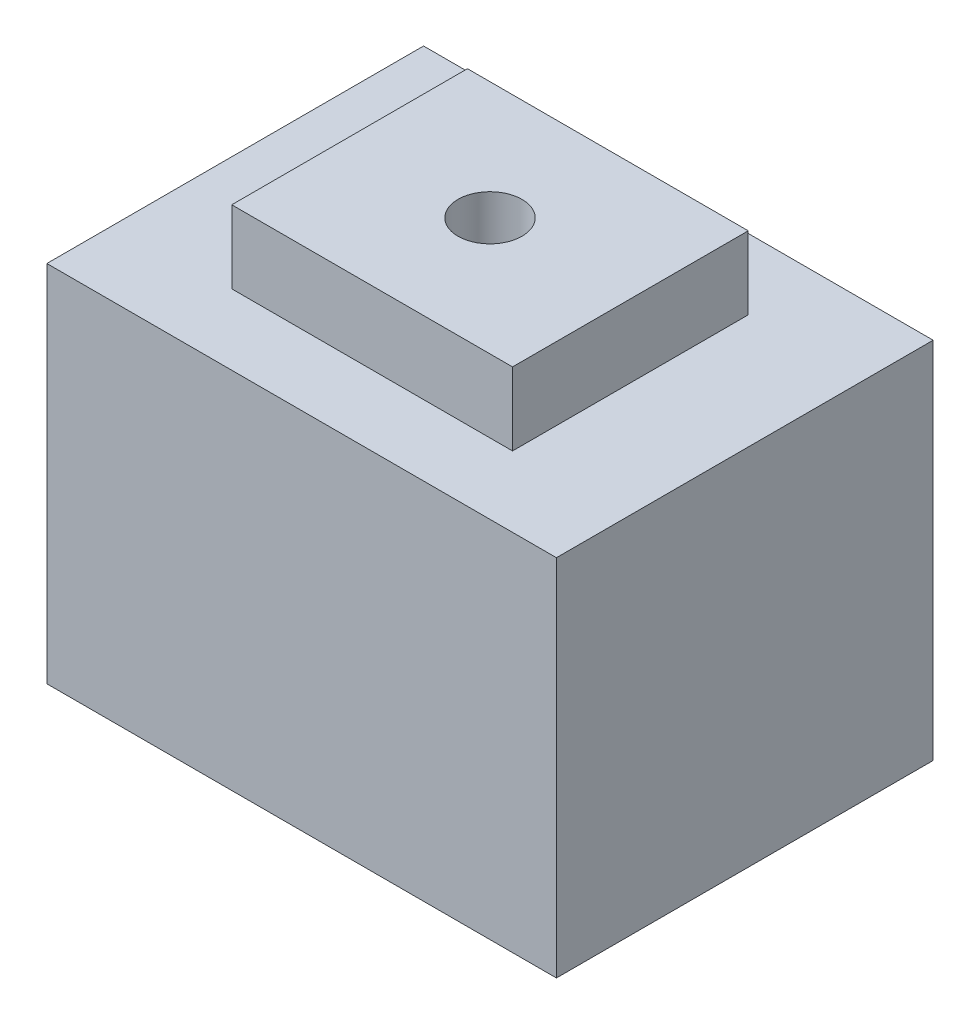
SolidWorks part; units mm, degrees
ref_plane "Front Plane" through (0, 0, 0) normal (0, 0, 1) x (1, 0, 0)
ref_plane "Top Plane" through (0, 0, 0) normal (0, 1, 0) x (1, 0, 0)
ref_plane "Right Plane" through (0, 0, 0) normal (1, 0, 0) x (0, 0, -1)
sketch "Sketch3" plane through (0, 0, 0) normal (0, 1, 0) x (1, 0, 0)
  line L1 (-35, -25.8732) -> (35, -25.8732)
  line L2 (-35, -25.8732) -> (-35, 25.8732)
  line L3 (-35, 25.8732) -> (35, 25.8732)
  line L4 (35, -25.8732) -> (35, 25.8732)
  line L5 (-35, -25.8732) -> (35, 25.8732) construction
  line L6 (-35, 25.8732) -> (35, -25.8732) construction
  point P0 (0, 0)
  dimension "D1" = 70
extrude "Boss-Extrude4" add sketch "Sketch3" along normal blind 50
sketch "Sketch5" plane through (0, 50, 0) normal (0, 1, 0) x (1, 0, 0)
  line L1 (-19.2845, 16.19) -> (19.2845, 16.19)
  line L2 (-19.2845, 16.19) -> (-19.2845, -16.19)
  line L3 (-19.2845, -16.19) -> (19.2845, -16.19)
  line L4 (19.2845, 16.19) -> (19.2845, -16.19)
  line L5 (-19.2845, 16.19) -> (19.2845, -16.19) construction
  line L6 (-19.2845, -16.19) -> (19.2845, 16.19) construction
  point P0 (0, 0)
extrude "Boss-Extrude5" add sketch "Sketch5" along normal blind 10
sketch "Sketch6" plane through (0, 0, 0) normal (0, -1, 0) x (1, 0, 0)
  circle A0 centre (0, 0) radius 8.8659
extrude "Cut-Extrude1" cut sketch "Sketch6" against normal blind 40
sketch "Sketch7" plane through (0, 40, 0) normal (0, -1, 0) x (1, 0, 0)
  circle A0 centre (0, 0) radius 2.5416
extrude "Cut-Extrude2" cut sketch "Sketch7" against normal blind 5
sketch "Sketch8" plane through (0, 60, 0) normal (0, 1, 0) x (1, 0, 0)
  circle A0 centre (0, 0) radius 4.3944
extrude "Cut-Extrude3" cut sketch "Sketch8" against normal through all
cosmetic thread "Cosmetic Thread2" parameters "D1"=5, "D2"=10
